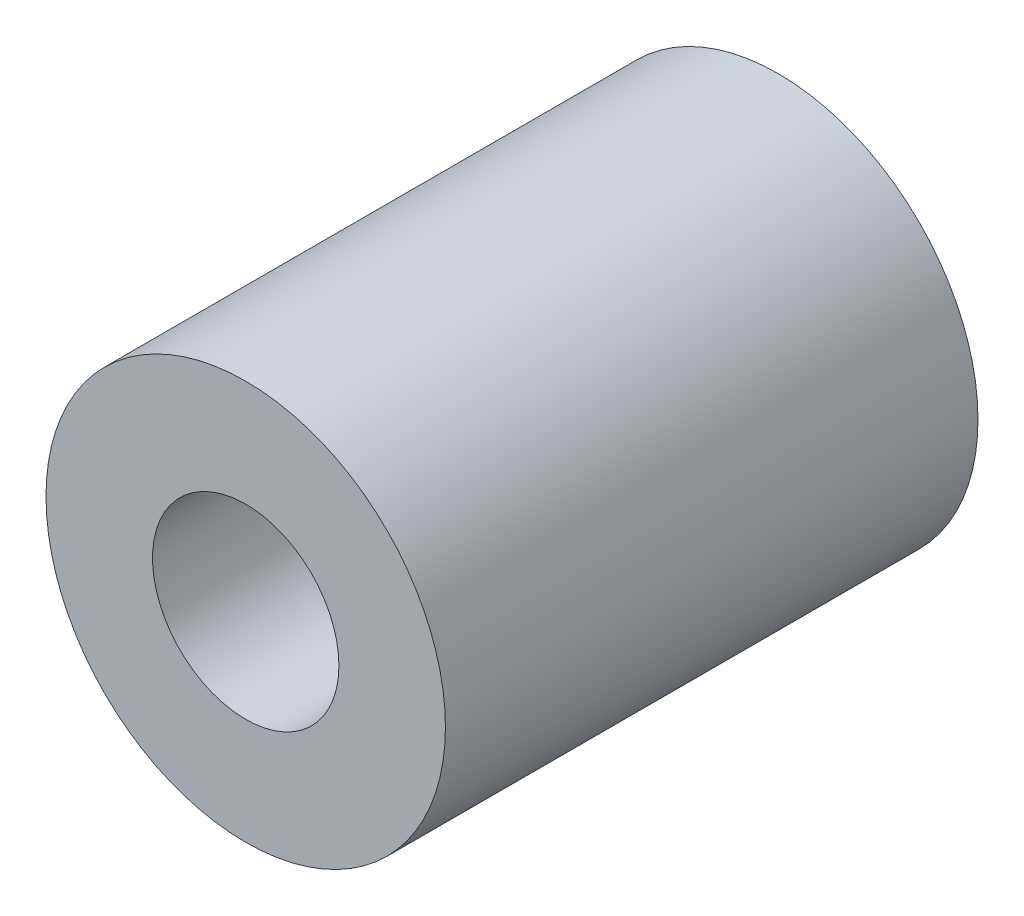
SolidWorks part; units mm, degrees
ref_plane "Plan de face" through (0, 0, 0) normal (0, 0, 1) x (1, 0, 0)
ref_plane "Plan de dessus" through (0, 0, 0) normal (0, 1, 0) x (1, 0, 0)
ref_plane "Plan de droite" through (0, 0, 0) normal (1, 0, 0) x (0, 0, -1)
sketch "Esquisse1" plane through (0, 0, 0) normal (0, 0, 1) x (1, 0, 0)
  circle A0 centre (0, 0) radius 1.75
  circle A1 centre (0, 0) radius 3.75
extrude "Boss.-Extru.1" add sketch "Esquisse1" along normal blind 10
